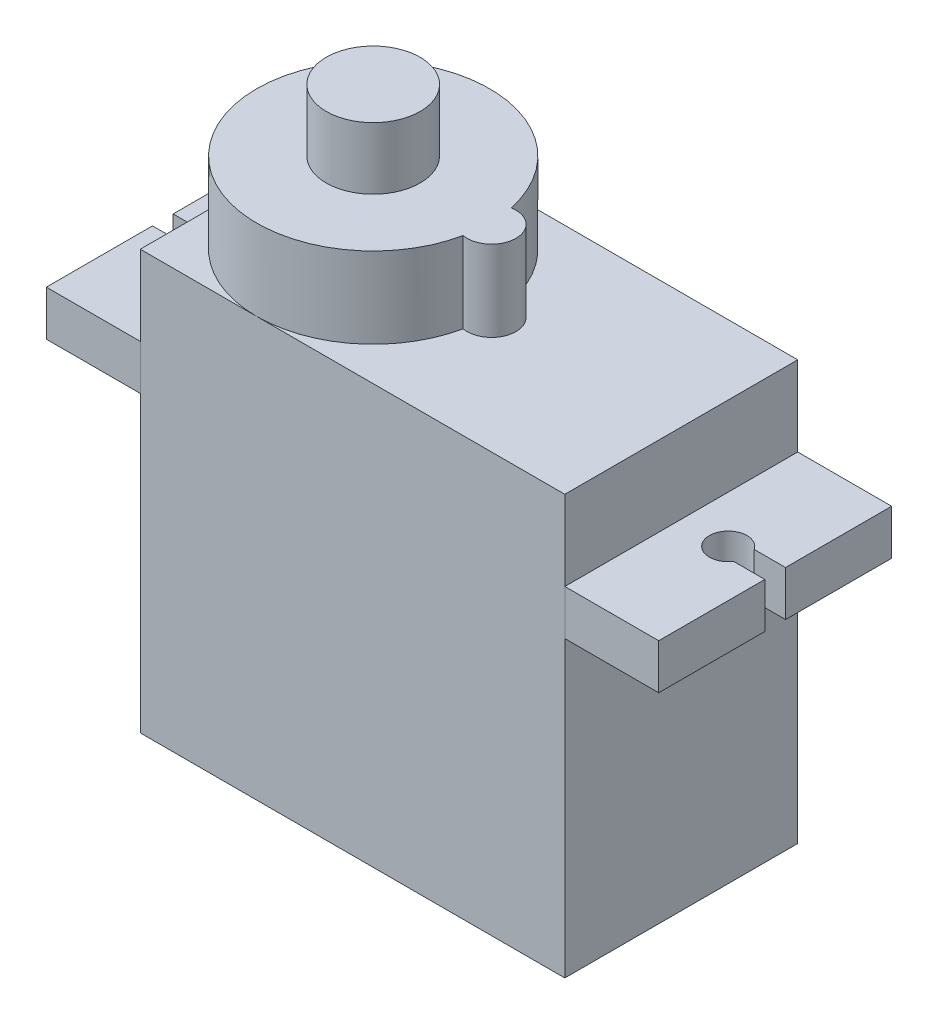
SolidWorks part; units mm, degrees
ref_plane "Front Plane" through (0, 0, 0) normal (0, 0, 1) x (1, 0, 0)
ref_plane "Top Plane" through (0, 0, 0) normal (0, 1, 0) x (1, 0, 0)
ref_plane "Right Plane" through (0, 0, 0) normal (1, 0, 0) x (0, 0, -1)
sketch "Sketch1" plane through (0, 0, 0) normal (0, 1, 0) x (1, 0, 0)
  line L1 (-11.3, -6.2) -> (11.3, -6.2)
  line L2 (-11.3, -6.2) -> (-11.3, 6.2)
  line L3 (-11.3, 6.2) -> (11.3, 6.2)
  line L4 (11.3, -6.2) -> (11.3, 6.2)
  line L5 (-11.3, -6.2) -> (11.3, 6.2) construction
  line L6 (-11.3, 6.2) -> (11.3, -6.2) construction
  point P0 (0, 0)
  dimension "D1" = 22.6
  dimension "D2" = 12.4
extrude "Boss-Extrude1" add sketch "Sketch1" along normal blind 22.3
sketch "Sketch2" plane through (11.3, 0, 0) normal (1, 0, 0) x (0, 0, -1)
  line L0 (-6.2, 22.3) -> (-6.2, 0) construction
  line L1 (-6.2, 18.05) -> (6.2, 18.05)
  line L2 (-6.2, 18.05) -> (-6.2, 15.65)
  line L3 (-6.2, 15.65) -> (6.2, 15.65)
  line L4 (6.2, 18.05) -> (6.2, 15.65)
  line L5 (6.2, 22.3) -> (6.2, 0) construction
  line L6 (-6.2, 22.3) -> (6.2, 22.3) construction
  dimension "D1" = 4.25
  dimension "D2" = 2.4
extrude "Boss-Extrude2" add sketch "Sketch2" along normal blind 5 separate body
sketch "Sketch3" plane through (-11.3, 0, 0) normal (-1, 0, 0) x (0, 0, 1)
  line L4 (6.2, 15.65) -> (6.2, 18.05)
  line L5 (-6.2, 15.65) -> (6.2, 15.65)
  line L6 (-6.2, 18.05) -> (-6.2, 15.65)
  line L7 (6.2, 18.05) -> (-6.2, 18.05)
  line L8 (6.2, 15.65) -> (6.2, 18.05)
  line L9 (-6.2, 15.65) -> (6.2, 15.65)
  line L10 (-6.2, 18.05) -> (-6.2, 15.65)
  line L11 (6.2, 18.05) -> (-6.2, 18.05)
  dimension "D1" = 0
extrude "Boss-Extrude3" add sketch "Sketch3" along normal blind 5 separate body
sketch "Sketch4" plane through (0, 18.05, 0) normal (0, 1, 0) x (1, 0, 0)
  line L0 (-16.3, -6.2) -> (-16.3, 6.2) construction
  line L1 (16.3, 6.2) -> (16.3, -6.2) construction
  line L3 (-16.3, 0.55) -> (-14.6352, 0.55)
  line L4 (-16.3, 0.55) -> (-16.3, -0.55)
  line L5 (-16.3, -0.55) -> (-14.6352, -0.55)
  line L7 (16.3, -0.55) -> (14.6352, -0.55)
  line L8 (16.3, -0.55) -> (16.3, 0.55)
  line L9 (16.3, 0.55) -> (14.6352, 0.55)
  arc A0 (-14.6352, -0.55) -> (-14.6352, 0.55) centre (-13.8, 0) ccw
  arc A1 (14.6352, 0.55) -> (14.6352, -0.55) centre (13.8, 0) ccw
  dimension "D1" = 2
  dimension "D2" = 2
  dimension "D4" = 2.5
  dimension "D3" = 2.5
  dimension "D5" = 1.1
  dimension "D6" = 0.55
  dimension "D7" = 1.1
  dimension "D8" = 0.55
extrude "Cut-Extrude1" cut sketch "Sketch4" against normal up to next (2.4 mm away)
sketch "Sketch5" plane through (0, 18.05, 0) normal (0, 1, 0) x (1, 0, 0)
  line L0 (16.3, 6.2) -> (16.3, -6.2) construction
  line L1 (14.6352, 0.55) -> (16.3, 0.55)
  line L3 (14.6352, -0.55) -> (16.3, -0.55)
  line L4 (16.3, 0.55) -> (16.3, -0.55)
  arc A0 (14.6352, 0.55) -> (14.6352, -0.55) centre (13.8, 0) ccw
  dimension "D1" = 2
  dimension "D2" = 1.1
  dimension "D3" = 0.55
  dimension "D4" = 2.5
extrude "Cut-Extrude2" cut sketch "Sketch5" against normal up to next (2.4 mm away) contours L1 L4 L3 A0
sketch "Sketch6" plane through (0, 22.3, 0) normal (0, 1, 0) x (1, 0, 0)
  line L0 (-11.3, 6.2) -> (-11.3, -6.2) construction
  line L1 (1.2, 1.3) -> (0.9622, 1.3)
  line L2 (1.2, -1.3) -> (0.9622, -1.3)
  arc A0 (0.9667, 1.2789) -> (0.9667, -1.2789) centre (-5.1, 0) ccw
  arc A1 (0.9667, -1.2789) -> (0.9667, 1.2789) centre (1.2, 0) ccw
  dimension "D2" = 12.4
  dimension "D3" = 2.6
  dimension "D1" = 6.2
  dimension "D4" = 6.3
extrude "Boss-Extrude4" add sketch "Sketch6" along normal blind 4.3 contours A1 A0
sketch "Sketch7" plane through (0, 26.6, 0) normal (0, 1, 0) x (1, 0, 0)
  circle A0 centre (-5.1, 0) radius 2.5
  dimension "D1" = 5
extrude "Boss-Extrude5" add sketch "Sketch7" along normal blind 3.3
sketch "Sketch8" plane through (-11.3, 0, 0) normal (-1, 0, 0) x (0, 0, 1)
  line L0 (-6.2, 0) -> (6.2, 0) construction
  circle A0 centre (-1.2, 4.5) radius 0.6
  circle A1 centre (0, 4.5) radius 0.6
  circle A2 centre (1.2, 4.5) radius 0.6
  dimension "D1" = 4.5
  dimension "D2" = 1.2
  dimension "D3" = 1.2
  dimension "D4" = 1.2
extrude "Boss-Extrude7" add sketch "Sketch8" along normal blind 2.3 separate body contours A1 | A0 | A2
